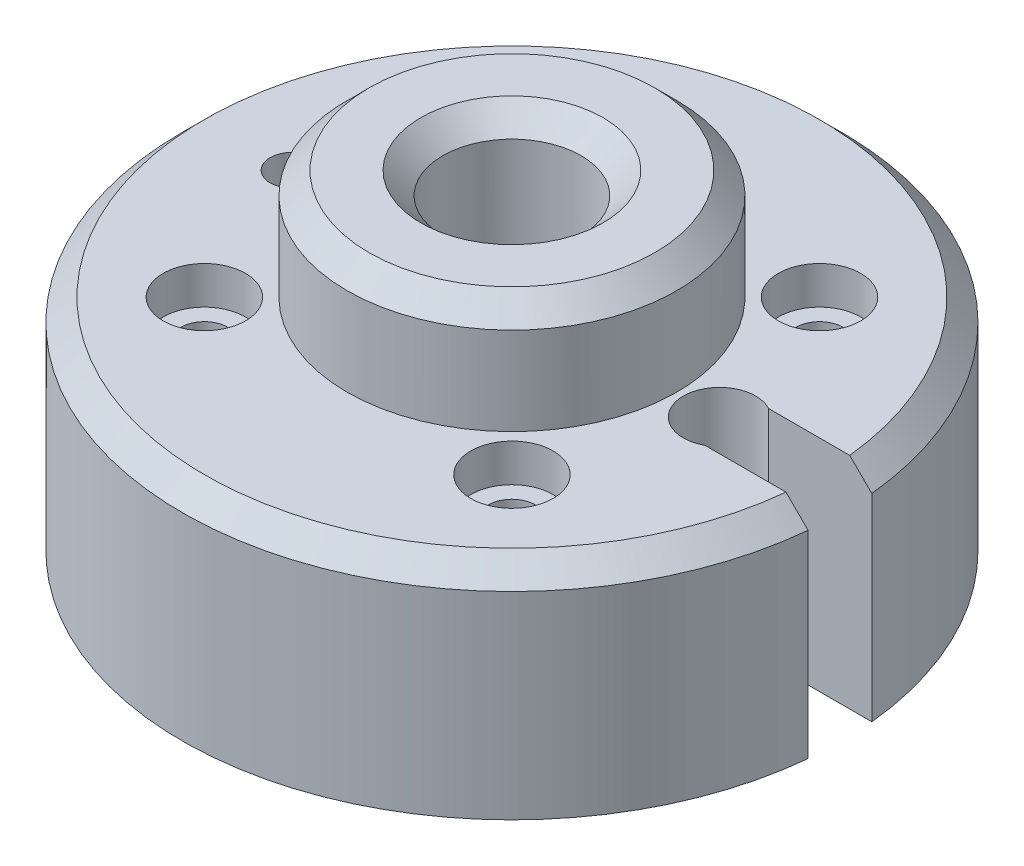
SolidWorks part; units mm, degrees
material "ABS PLASTIC"
ref_plane "Front Plane" through (0, 0, 0) normal (0, 0, 1) x (1, 0, 0)
ref_plane "Top Plane" through (0, 0, 0) normal (0, 1, 0) x (1, 0, 0)
ref_plane "Right Plane" through (0, 0, 0) normal (1, 0, 0) x (0, 0, -1)
sketch "Sketch1" plane through (0, 0, 0) normal (0, 0, 1) x (1, 0, 0)
  line L0 (4, 19.05) -> (9.525, 19.05)
  line L1 (9.525, 19.05) -> (9.525, 12.7)
  line L2 (9.525, 12.7) -> (19.05, 12.7)
  line L3 (19.05, 12.7) -> (19.05, 0)
  line L4 (19.05, 0) -> (4, 0)
  line L5 (4, 0) -> (4, 19.05)
  line L6 (0, 24.6003) -> (0, -9.0595) construction
  dimension "D1" = 38.1
  dimension "D2" = 12.7
  dimension "D3" = 6.35
  dimension "D4" = 8
  dimension "D5" = 19.05
revolve "Revolve1" add sketch "Sketch1" angle 360 about L6
chamfer "Chamfer1" distance 1.27 angle 45 3 edges at (0, 12.7, 19.05) (0, 19.05, 9.525) (0, 19.05, 4)
hole_wizard "CBORE for #2 Socket Head Cap Screw1" positions "Sketch2" profile "Sketch3" counterbore size "#2" standard "ANSI Inch" end condition up to next
sketch "Sketch2" plane through (0, 12.7, 0) normal (0, 1, 0) x (1, 0, 0)
  line L1 (-8.89, 8.89) -> (8.89, 8.89)
  line L2 (-8.89, 8.89) -> (-8.89, -8.89)
  line L3 (-8.89, -8.89) -> (8.89, -8.89)
  line L4 (8.89, 8.89) -> (8.89, -8.89)
  point P0 (-8.89, -8.89)
  point P2 (8.89, -8.89)
  point P4 (8.89, 8.89)
  point P6 (-8.89, 8.89)
  point P38 (0, 8.89)
  point P40 (-8.89, 0)
  dimension "D1" = 17.78
  dimension "D2" = 17.78
sketch "Sketch3" plane through (-8.89, 12.7, 8.89) normal (1, 0, 0) x (0, 0, 1)
  line L0 (0, 0) -> (0, 12.7)
  line L1 (0, 12.7) -> (1.3525, 12.7)
  line L3 (1.3525, 12.7) -> (1.3525, 2.1844)
  line L4 (1.3525, 2.1844) -> (2.3812, 2.1844)
  line L5 (2.3812, 2.1844) -> (2.3812, 0)
  line L7 (2.3812, 0) -> (0, 0)
  line L11 (0, -6.35) -> (0, 107.95) construction
  dimension "Thru Hole Dia." = 2.7051
  dimension "Thru Hole Depth" = 12.7
  dimension "C'Bore Dia." = 4.7625
  dimension "C'Bore Depth" = 2.1844
sketch "Sketch6" plane through (0, 12.7, 0) normal (0, 1, 0) x (1, 0, 0)
  line L0 (13, 1.8415) -> (18.9608, 1.8415)
  line L1 (13, -1.8415) -> (18.9608, -1.8415)
  line L2 (-24.1594, 0) -> (27.0079, 0) construction
  arc A0 (13, 1.8415) -> (13, -1.8415) centre (12, 0) ccw
  circle A1 centre (0, 0) radius 19.05 construction
  arc A2 (18.9608, -1.8415) -> (18.9608, 1.8415) centre (0, 0) ccw
  dimension "D1" = 4.191
  dimension "D2" = 12
  dimension "D3" = 3.683
extrude "Cut-Extrude1" cut sketch "Sketch6" against normal through all
sketch "Sketch7" plane through (0, 12.7, 0) normal (0, 1, 0) x (1, 0, 0)
  line L0 (26.2776, 0) -> (-28.5295, 0) construction
  circle A0 centre (-12.7, 0) radius 1.27
  dimension "D1" = 12.7
  dimension "D2" = 2.54
extrude "Cut-Extrude2" cut sketch "Sketch7" against normal through all
